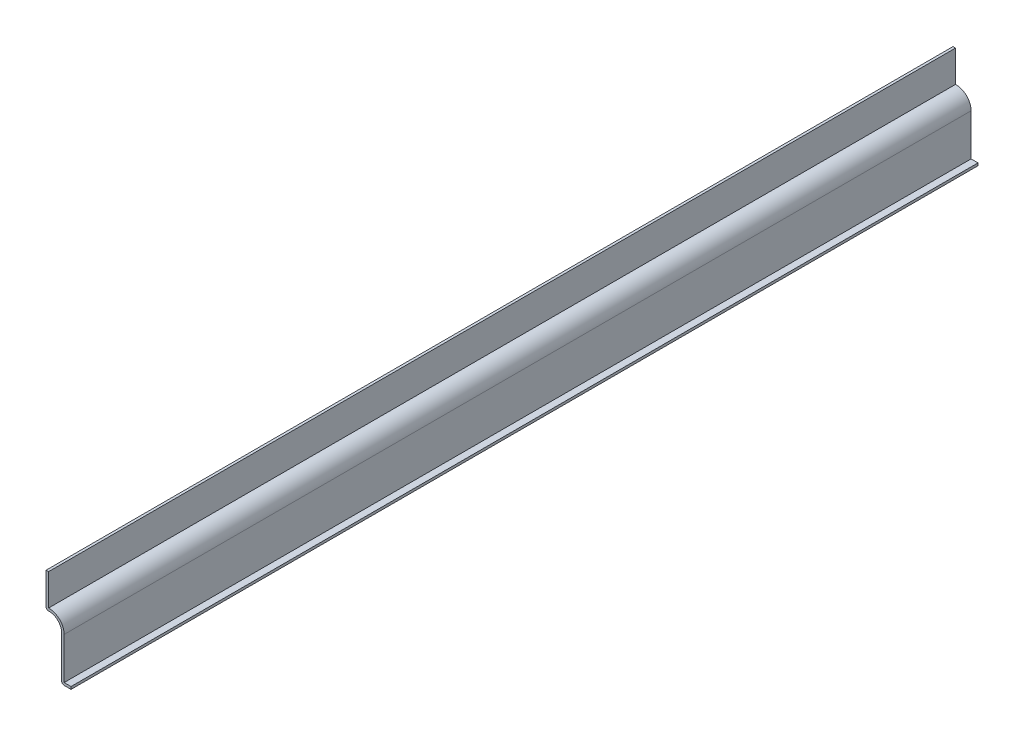
SolidWorks part; units mm, degrees
ref_plane "Front Plane" through (0, 0, 0) normal (0, 0, 1) x (1, 0, 0)
ref_plane "Top Plane" through (0, 0, 0) normal (0, 1, 0) x (1, 0, 0)
ref_plane "Right Plane" through (0, 0, 0) normal (1, 0, 0) x (0, 0, -1)
sketch "Sketch1" plane through (0, 0, 0) normal (0, 0, 1) x (1, 0, 0)
  line L0 (0, 0) -> (-4.7625, 0)
  line L1 (-4.7625, 0) -> (-4.7625, 22.4266)
  line L2 (-12.7, 28.575) -> (-12.7, 46.0375)
  arc A0 (-4.7625, 22.4266) -> (-12.7, 28.575) centre (-11.1125, 22.4266) ccw
  dimension "D3" = 6.35
  dimension "D1" = 46.0375
  dimension "D2" = 17.4625
  dimension "D4" = 7.9375
  dimension "D5" = 28.575
  dimension "D6" = 4.7625
extrude "Extrude-Thin1" add sketch "Sketch1" against normal blind 460.375 thin
fillet "Fillet1" radius 1.27 2 edges at (-4.7625, 0, -230.1875) (-12.7, 28.575, -230.1875)
